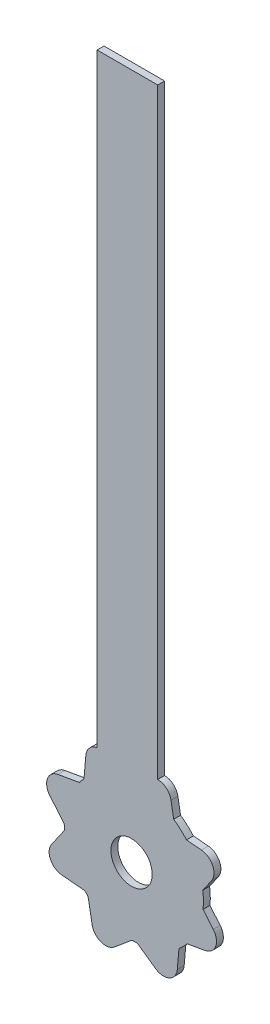
SolidWorks part; units mm, degrees
material "3003 Alaşım"
ref_plane "Ön Düzlem" through (0, 0, 0) normal (0, 0, 1) x (1, 0, 0)
ref_plane "Üst Düzlem" through (0, 0, 0) normal (0, 1, 0) x (1, 0, 0)
ref_plane "Sağ Düzlem" through (0, 0, 0) normal (1, 0, 0) x (0, 0, -1)
sketch "Çizim1" plane through (0, 0, 0) normal (0, 0, 1) x (1, 0, 0)
  line L0 (-16.2005, -56.8603) -> (-16.2005, 33.1397)
  line L31 (-25, 33.1397) -> (-25, -57.8833)
  line L33 (-25, 33.1397) -> (-16.2005, 33.1397)
  line L34 (-24.5649, -66.2773) -> (-14.5649, -66.2773) construction
  arc A18 (-25, -57.8833) -> (-16.2005, -56.8603) centre (-19.5649, -66.2773) ccw
  circle A22 centre (-19.5649, -66.2773) radius 5
  dimension "D1" = 90
  dimension "D9" = 10
extrude "Yükseklik-Ekstrüzyon2" add sketch "Çizim1" along normal blind 1
sketch "Çizim2" plane through (0, 0, 1) normal (0, 0, 1) x (1, 0, 0)
  line L0 (-14.2682, -55.8596) -> (-13.7465, -58.818)
  line L17 (-25.7318, -77.2275) -> (-26.2535, -74.2691)
  line L18 (-16.5798, -57.1466) -> (-14.8697, -52.4482) construction
  line L19 (-26.6412, -56.3999) -> (-26.903, -59.3924)
  line L20 (-30.6839, -60.8117) -> (-27.7256, -60.2901)
  line L21 (-8.1313, -69.0202) -> (-10.0622, -66.719)
  line L22 (-9.3161, -72.2754) -> (-12.2744, -72.797)
  line L23 (-8.3923, -63.0419) -> (-10.1153, -65.5026)
  line L24 (-13.3588, -76.6873) -> (-13.097, -73.6947)
  line L25 (-22.4766, -78.4123) -> (-20.1754, -76.4813)
  line L26 (-17.5234, -54.6749) -> (-19.8246, -56.6058)
  line L27 (-31.8687, -64.0669) -> (-29.9378, -66.3681)
  line L28 (-23.5016, -54.9359) -> (-21.0409, -56.6589)
  line L29 (-30.1437, -73.1848) -> (-27.1511, -73.4466)
  line L30 (-16.4984, -78.1513) -> (-18.9591, -76.4282)
  line L31 (-31.6077, -70.0452) -> (-29.8847, -67.5845)
  line L32 (-9.8563, -59.9024) -> (-12.8489, -59.6406)
  arc A38 (-25.7318, -77.2275) -> (-22.4766, -78.4123) centre (-23.7622, -76.8802) ccw
  arc A39 (-13.097, -73.6947) -> (-12.2744, -72.797) centre (-12.1008, -73.7818) cw
  arc A40 (-8.3923, -63.0419) -> (-9.8563, -59.9024) centre (-10.0306, -61.8948) ccw
  arc A41 (-27.7256, -60.2901) -> (-26.903, -59.3924) centre (-27.8992, -59.3053) ccw
  arc A42 (-23.5016, -54.9359) -> (-26.6412, -56.3999) centre (-24.6488, -56.5742) ccw
  arc A43 (-14.2682, -55.8596) -> (-17.5234, -54.6749) centre (-16.2378, -56.2069) ccw
  arc A44 (-31.6077, -70.0452) -> (-30.1437, -73.1848) centre (-29.9694, -71.1924) ccw
  arc A45 (-10.0622, -66.719) -> (-10.1153, -65.5026) centre (-9.2962, -66.0762) cw
  circle A46 centre (-20, -66.5436) radius 10 construction
  arc A47 (-16.4984, -78.1513) -> (-13.3588, -76.6873) centre (-15.3512, -76.5129) ccw
  arc A48 (-29.8847, -67.5845) -> (-29.9378, -66.3681) centre (-30.7038, -67.0109) ccw
  arc A49 (-12.8489, -59.6406) -> (-13.7465, -58.818) centre (-12.7617, -58.6444) cw
  arc A50 (-19.8246, -56.6058) -> (-21.0409, -56.6589) centre (-20.4673, -55.8397) cw
  arc A51 (-20.1754, -76.4813) -> (-18.9591, -76.4282) centre (-19.5327, -77.2474) cw
  arc A52 (-30.6839, -60.8117) -> (-31.8687, -64.0669) centre (-30.3366, -62.7813) ccw
  arc A53 (-27.1511, -73.4466) -> (-26.2535, -74.2691) centre (-27.2383, -74.4428) cw
  arc A54 (-9.3161, -72.2754) -> (-8.1313, -69.0202) centre (-9.6634, -70.3058) ccw
  circle A55 centre (-20, -66.5436) radius 3
  point P0 (0, 0)
  point P48 (-20, -66.5436)
extrude "Yükseklik-Ekstrüzyon4" add sketch "Çizim2" against normal blind 1
